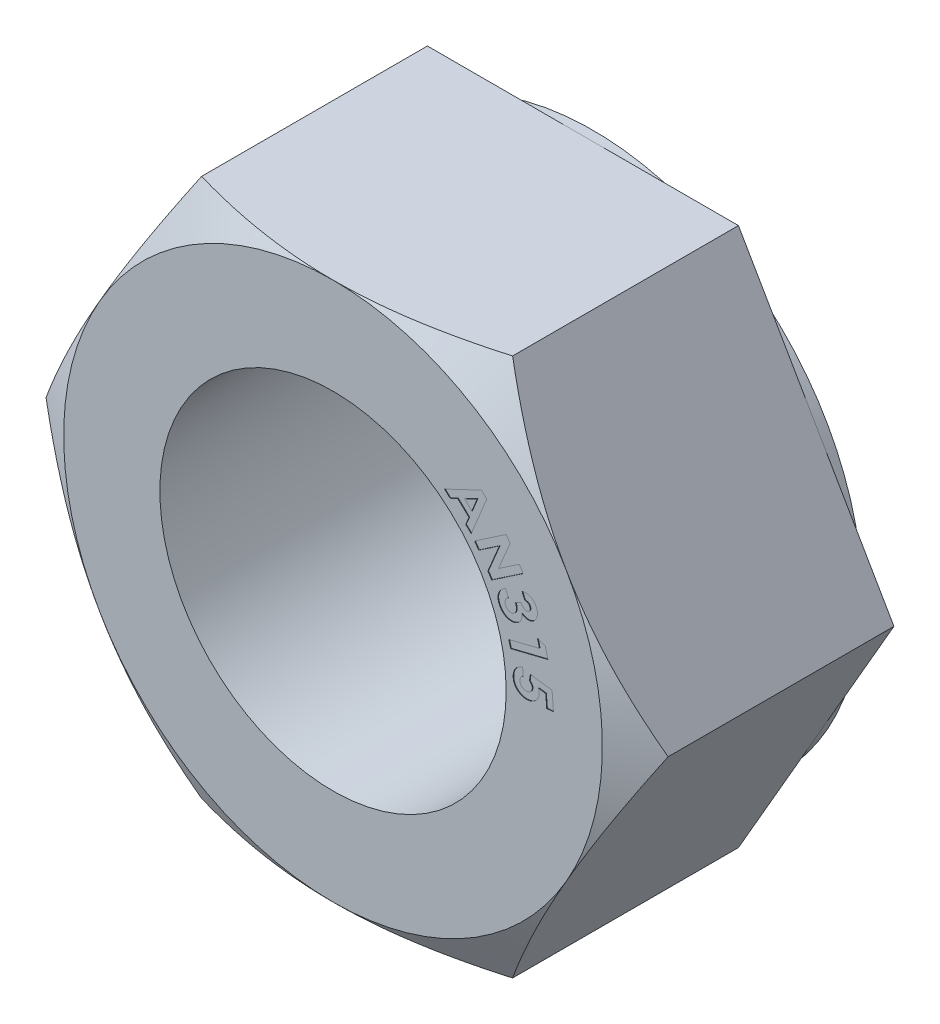
SolidWorks part; units mm, degrees
material "AISI 4130 Steel, normalized at 870C"
ref_plane "Front Plane" through (0, 0, 0) normal (0, 0, 1) x (1, 0, 0)
ref_plane "Top Plane" through (0, 0, 0) normal (0, 1, 0) x (1, 0, 0)
ref_plane "Right Plane" through (0, 0, 0) normal (1, 0, 0) x (0, 0, -1)
sketch "Sketch1" plane through (0, 0, 0) normal (0, 0, 1) x (1, 0, 0)
  line L1 (6.4158, 11.1125) -> (-6.4158, 11.1125)
  line L2 (-6.4158, 11.1125) -> (-12.8316, 0)
  line L3 (-12.8316, 0) -> (-6.4158, -11.1125)
  line L4 (-6.4158, -11.1125) -> (6.4158, -11.1125)
  line L5 (6.4158, -11.1125) -> (12.8316, 0)
  line L6 (12.8316, 0) -> (6.4158, 11.1125)
  circle A0 centre (0, 0) radius 11.1125 construction
  circle A1 centre (0, 0) radius 7.1438
  dimension "Diameter A" = 22.225
  dimension "T - Thread" = 14.2875
extrude "Boss-Extrude1" add sketch "Sketch1" along normal blind 10.7156
sketch "Sketch2" plane through (0, 0, 10.7156) normal (0, 0, 1) x (1, 0, 0)
  line L0 (12.8316, 0) -> (6.4158, 11.1125) construction
  circle A0 centre (0, 0) radius 11.1125
extrude "Cut-Extrude1" cut sketch "Sketch2" against normal blind 3.5719 draft 60 flip side to cut
sketch "Sketch3" plane through (0, 0, 0) normal (0, 0, -1) x (-1, 0, 0)
  line L0 (-12.8316, 0) -> (-6.4158, 11.1125) construction
  circle A0 centre (0, 0) radius 11.1125
  circle A1 centre (0, 0) radius 7.1438
  circle A2 centre (0, 0) radius 7.1438 construction
sketch "Sketch4" plane through (0, 0, 10.7156) normal (0, 0, 1) x (1, 0, 0)
  circle A0 centre (0, 0) radius 7.5248 construction
  circle A1 centre (0, 0) radius 7.1438 construction
  text T0 "AN315" font "Century Gothic" height in points 6
  dimension "D1" = 0.381
extrude "Cut-Extrude2" cut sketch "Sketch4" against normal blind 0.0254
sketch "Sketch6" plane through (0, 0, 0) normal (0, 0, -1) x (-1, 0, 0)
  line L0 (6.4158, 11.1125) -> (12.8316, 0) construction
  circle A0 centre (0, 0) radius 11.1125
  circle A1 centre (0, 0) radius 12.8316
extrude "Cut-Extrude4" cut sketch "Sketch6" against normal blind 0.4064
